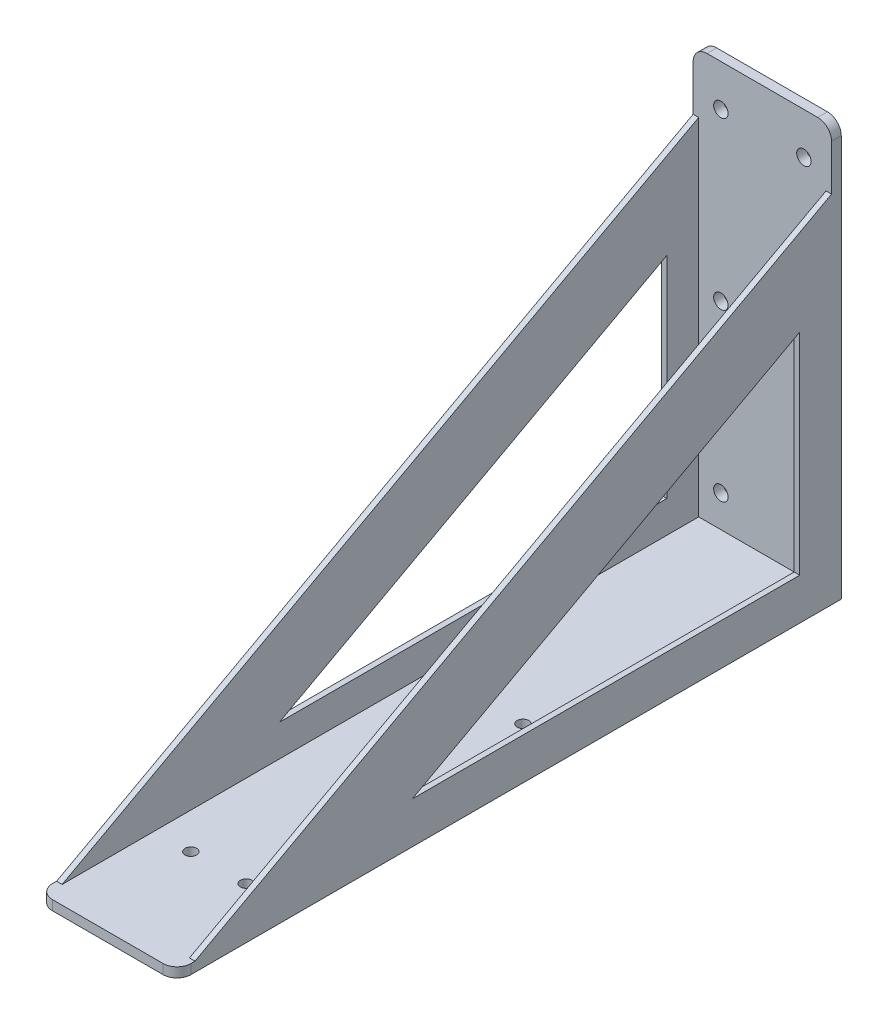
SolidWorks part; units mm, degrees
ref_plane "前视基准面" through (0, 0, 0) normal (0, 0, 1) x (1, 0, 0)
ref_plane "上视基准面" through (0, 0, 0) normal (0, 1, 0) x (1, 0, 0)
ref_plane "右视基准面" through (0, 0, 0) normal (1, 0, 0) x (0, 0, -1)
sketch "草图1" plane through (0, 0, 0) normal (1, 0, 0) x (0, 0, -1)
  line L0 (-240, 0) -> (0, 0)
  line L1 (0, 0) -> (0, 150)
  line L2 (0, 150) -> (-3.5, 150)
  line L3 (-3.5, 150) -> (-3.5, 3.5)
  line L4 (-3.5, 3.5) -> (-240, 3.5)
  line L5 (-240, 3.5) -> (-240, 0)
  dimension "D1" = 3.5
  dimension "D2" = 3.5
  dimension "D3" = 240
  dimension "D4" = 150
extrude "凸台-拉伸1" add sketch "草图1" along normal mid plane 50
sketch "草图4" plane through (0, 0, 0) normal (0, 0, -1) x (-1, 0, 0)
  line L0 (-25, 150) -> (25, 0) construction
  line L1 (25, 150) -> (-25, 0) construction
  line L2 (0, 75) -> (0, 102.8178) construction
  line L3 (0, 75) -> (-48.8805, 75) construction
  line L4 (-15, 135) -> (-15, 75) construction
  line L5 (-15, 75) -> (15, 75) construction
  line L6 (15, 75) -> (15, 135) construction
  circle A0 centre (-15, 135) radius 2.6
  circle A1 centre (15, 135) radius 2.6
  circle A2 centre (15, 15) radius 2.6
  circle A3 centre (-15, 15) radius 2.6
  circle A4 centre (-15, 75) radius 2.6
  circle A5 centre (15, 75) radius 2.6
  dimension "D3" = 5.2
  dimension "D4" = 5.2
  dimension "D5" = 5.2
  dimension "D1" = 120
  dimension "D2" = 30
extrude "切除-拉伸2" cut sketch "草图4" against normal through all
fillet "圆角1" radius 5 2 edges at (25, 1.75, 240) (-25, 1.75, 240)
fillet "圆角2" radius 5 2 edges at (25, 150, 1.75) (-25, 150, 1.75)
sketch "草图5" plane through (0, 0, 0) normal (0, -1, 0) x (1, 0, 0)
  line L0 (0, 0) -> (0, 244.4973) construction
  line L1 (-10, 200) -> (-10, 100) construction
  line L2 (25, 0) -> (-25, 0) construction
  circle A0 centre (-10, 200) radius 2.1
  circle A1 centre (-10, 100) radius 2.1
  circle A2 centre (10, 100) radius 2.1
  circle A3 centre (10, 200) radius 2.1
  dimension "D1" = 4.2
  dimension "D2" = 4.2
  dimension "D3" = 100
  dimension "D4" = 100
  dimension "D5" = 20
extrude "切除-拉伸3" cut sketch "草图5" against normal through all
sketch "草图8" plane through (25, 0, 0) normal (1, 0, 0) x (0, 0, -1)
  line L0 (-3.5, 3.5) -> (-233.5, 3.5)
  line L1 (-3.5, 3.5) -> (-235, 3.5) construction
  line L2 (-233.5, 3.5) -> (-3.5, 128.5)
  line L3 (-3.5, 145) -> (-3.5, 3.5) construction
  line L4 (-3.5, 128.5) -> (-3.5, 3.5)
  dimension "D1" = 230
  dimension "D2" = 125
extrude "凸台-拉伸2" add sketch "草图8" against normal blind 2
sketch "草图9" plane through (-25, 0, 0) normal (-1, 0, 0) x (0, 0, 1)
  line L3 (3.5, 3.5) -> (233.5, 3.5)
  line L4 (233.5, 3.5) -> (3.5, 128.5)
  line L5 (3.5, 128.5) -> (3.5, 3.5)
  line L6 (3.5, 3.5) -> (233.5, 3.5)
  line L7 (233.5, 3.5) -> (3.5, 128.5)
  line L8 (3.5, 128.5) -> (3.5, 3.5)
  dimension "D1" = 0
extrude "凸台-拉伸3" add sketch "草图9" against normal blind 2
sketch "草图10" plane through (-25, 0, 0) normal (-1, 0, 0) x (0, 0, 1)
  line L2 (15, 91.087) -> (15, 15)
  line L4 (15, 15) -> (155, 15)
  line L5 (155, 15) -> (15, 91.087)
  line L6 (233.5, 3.5) -> (3.5, 128.5) construction
  line L7 (0, 0) -> (0, 145) construction
  line L8 (235, 0) -> (0, 0) construction
  dimension "D1" = 15
  dimension "D2" = 15
  dimension "D3" = 140
extrude "切除-拉伸4" cut sketch "草图10" against normal through all
